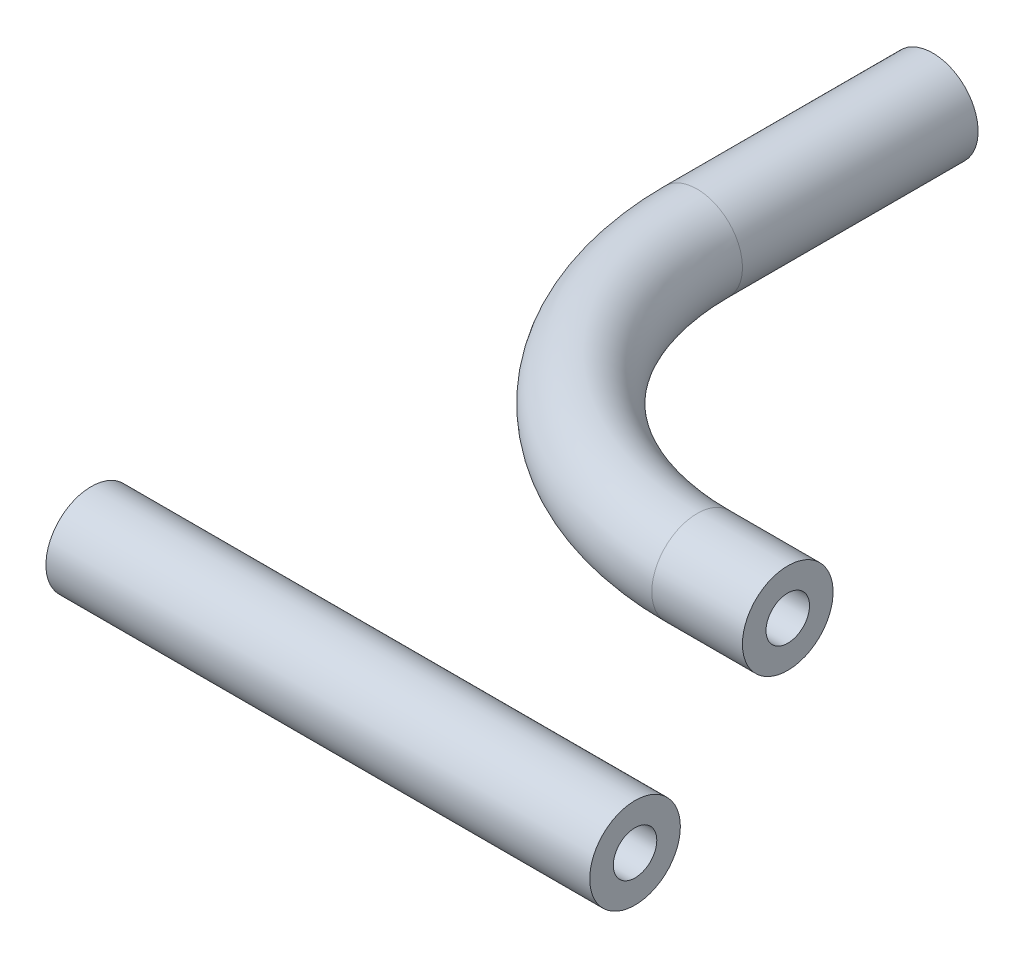
SolidWorks part; units mm, degrees
ref_plane "Front Plane" through (0, 0, 0) normal (0, 0, 1) x (1, 0, 0)
ref_plane "Top Plane" through (0, 0, 0) normal (0, 1, 0) x (1, 0, 0)
ref_plane "Right Plane" through (0, 0, 0) normal (1, 0, 0) x (0, 0, -1)
sketch "Sketch1" plane through (0, 0, 0) normal (0, 1, 0) x (1, 0, 0)
  line L0 (0, 22.86) -> (0, 39.37)
  line L1 (22.86, 0) -> (29.21, 0)
  arc A0 (22.86, 0) -> (0, 22.86) centre (22.86, 22.86) cw
  point P6 (0, 0)
  point P7 (0, 0)
  dimension "D1" = 22.86
  dimension "D2" = 6.35
  dimension "D3" = 16.51
sketch3d "3DSketch1"
sketch "Sketch2" plane through (29.21, 0, 0) normal (-1, 0, 0) x (0, 0, 1)
  circle A0 centre (-3.175, 0) radius 3.175
  circle A1 centre (-3.175, 0) radius 1.524
  point P4 (0, 0)
  point P6 (0, 0)
  dimension "D1" = 6.35
  dimension "D2" = 1.651
sweep "Sweep1" add profiles "Sketch2" path "Sketch1"
sketch "Sketch3" plane through (0, 0, 0) normal (1, 0, 0) x (0, 0, -1)
  circle A0 centre (-16.4145, 0) radius 3.175
  circle A1 centre (-16.4145, 0) radius 1.524
  circle A2 centre (3.175, 0) radius 3.175 construction
  circle A3 centre (3.175, 0) radius 1.524 construction
extrude "Boss-Extrude1" add sketch "Sketch3" along normal blind 38.1 separate body
